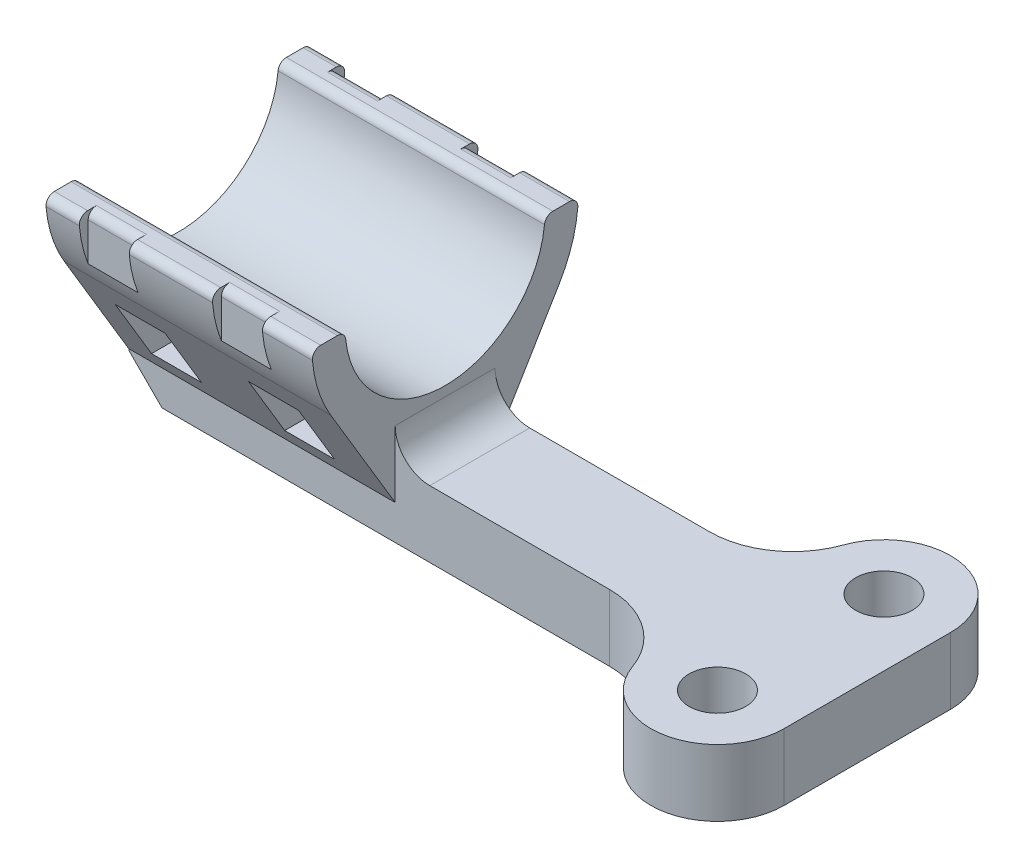
SolidWorks part; units mm, degrees
ref_plane "Front Plane" through (0, 0, 0) normal (0, 0, 1) x (1, 0, 0)
ref_plane "Top Plane" through (0, 0, 0) normal (0, 1, 0) x (1, 0, 0)
ref_plane "Right Plane" through (0, 0, 0) normal (1, 0, 0) x (0, 0, -1)
sketch "Sketch1" plane through (0, 0, 0) normal (0, 1, 0) x (1, 0, 0)
  line L0 (0, 0) -> (12.8697, 0)
  line L1 (0, 0) -> (0, 6)
  line L2 (0, 6) -> (12.8697, 6)
  line L3 (25.355, 8) -> (25.355, -2)
  arc A0 (12.8697, 6) -> (17.5838, 9.3333) centre (12.8697, 11) ccw
  arc A1 (25.355, 8) -> (17.5838, 9.3333) centre (21.355, 8) ccw
  arc A2 (17.5838, -3.3333) -> (25.355, -2) centre (21.355, -2) ccw
  arc A3 (17.5838, -3.3333) -> (12.8697, 0) centre (12.8697, -5) ccw
  circle A4 centre (21.355, -2) radius 1.7
  circle A5 centre (21.355, 8) radius 1.7
  dimension "D2" = 10
  dimension "D3" = 8
  dimension "D4" = 8
  dimension "D5" = 10
  dimension "D6" = 10
  dimension "D8" = 3.4
  dimension "D9" = 3.4
  dimension "D1" = 6
  dimension "D7" = 25.355
extrude "Boss-Extrude1" add sketch "Sketch1" along normal blind 4
sketch "Sketch2" plane through (0, 0, 0) normal (-1, 0, 0) x (0, 0, 1)
  line L0 (-6, 0) -> (0, 0)
  line L1 (0, 0) -> (0, 2.084)
  line L2 (0, 4) -> (0, 0) construction
  line L3 (-6, 0) -> (-6, 2.084)
  line L4 (-6, 4) -> (-6, 0) construction
  line L5 (-9.8672, 8.5551) -> (-6, 2.084)
  line L6 (0, 2.084) -> (3.8672, 8.5551)
  line L7 (-10.471, 12.5) -> (-9.4665, 12.5)
  line L8 (3.4665, 12.5) -> (4.471, 12.5)
  arc A0 (-8.9691, 12.0507) -> (2.9691, 12.0507) centre (-3, 12.659) ccw
  arc A1 (-10.9691, 11.9561) -> (-9.8672, 8.5551) centre (-3, 12.659) ccw
  arc A2 (3.8672, 8.5551) -> (4.9691, 11.9561) centre (-3, 12.659) ccw
  arc A3 (4.471, 12.5) -> (4.9691, 11.9561) centre (4.471, 12) cw
  arc A4 (2.9691, 12.0507) -> (3.4665, 12.5) centre (3.4665, 12) cw
  arc A5 (-8.9691, 12.0507) -> (-9.4665, 12.5) centre (-9.4665, 12) ccw
  arc A6 (-10.471, 12.5) -> (-10.9691, 11.9561) centre (-10.471, 12) ccw
  point P14 (-3, 0)
  point P22 (2.9979, 12.5)
  dimension "D2" = 12
  dimension "D3" = 12.659
  dimension "D4" = 16
  dimension "D6" = 0.5
  dimension "D1" = 2.084
  dimension "D5" = 12.5
extrude "Boss-Extrude2" add sketch "Sketch2" along normal blind 16
chamfer "Chamfer1" distance 2 angle 45 1 edges at (-16, 0, -3)
fillet "Fillet1" radius 2.08 1 edges at (0, 4, -3)
sketch "Sketch4" plane through (0, 0, 0) normal (0, 0, 1) x (1, 0, 0)
  line L0 (-16, 2.084) -> (-16, 8.5551) construction
  line L1 (-14, 5.289) -> (-11, 5.289)
  line L2 (-14, 5.289) -> (-14, 3.144)
  line L3 (-14, 3.144) -> (-11, 3.144)
  line L4 (-11, 5.289) -> (-11, 3.144)
  line L5 (-6, 5.289) -> (-3, 5.289)
  line L6 (-6, 5.289) -> (-6, 3.144)
  line L7 (-6, 3.144) -> (-3, 3.144)
  line L8 (-3, 5.289) -> (-3, 3.144)
  line L9 (-14, 0) -> (12.8697, 0) construction
  dimension "D1" = 3
  dimension "D2" = 3
  dimension "D3" = 2.145
  dimension "D4" = 2.145
  dimension "D5" = 2
  dimension "D6" = 5
  dimension "D7" = 3.144
  dimension "D8" = 3.144
extrude "Cut-Extrude1" cut sketch "Sketch4" against normal through all both and the other way through all
chamfer "Chamfer2" distance 1.705 angle 30 4 edges at (-12.5, 5.289, -7.9153) (-4.5, 5.289, -7.9153) (-4.5, 5.289, 1.9153) (-12.5, 5.289, 1.9153)
ref_plane "Plane3" through (-14, 0, 0) normal (-1, 0, 0) x (0, 0, 1)
sketch "Sketch5" plane through (-14, 0, 0) normal (-1, 0, 0) x (0, 0, 1)
  line L0 (4.439, 9.716) -> (4.439, 12)
  line L1 (4.471, 12.5) -> (3.4665, 12.5) construction
  line L2 (4.471, 12.5) -> (3.939, 12.5)
  line L3 (-9.939, 12.5) -> (-10.471, 12.5)
  line L4 (-9.4665, 12.5) -> (-10.471, 12.5) construction
  line L5 (-10.439, 12) -> (-10.439, 9.716)
  arc A0 (3.8672, 8.5551) -> (4.9691, 11.9561) centre (-3, 12.659) ccw construction
  arc A1 (4.439, 12) -> (3.939, 12.5) centre (3.939, 12) ccw
  arc A2 (4.9691, 11.9561) -> (4.471, 12.5) centre (4.471, 12) ccw construction
  arc A3 (4.439, 9.716) -> (4.9691, 11.9561) centre (-3, 12.659) ccw
  arc A4 (4.9691, 11.9561) -> (4.471, 12.5) centre (4.471, 12) ccw
  arc A5 (-10.9691, 11.9561) -> (-9.8672, 8.5551) centre (-3, 12.659) ccw construction
  arc A6 (-9.939, 12.5) -> (-10.439, 12) centre (-9.939, 12) ccw
  arc A7 (-10.471, 12.5) -> (-10.9691, 11.9561) centre (-10.471, 12) ccw construction
  arc A8 (-10.9691, 11.9561) -> (-10.439, 9.716) centre (-3, 12.659) ccw
  arc A9 (-10.471, 12.5) -> (-10.9691, 11.9561) centre (-10.471, 12) ccw
  point P10 (4.439, 12.5)
  point P21 (-10.439, 12.5)
  dimension "D3" = 0.5
  dimension "D5" = 0.5
  dimension "D1" = 90
  dimension "D2" = 2.784
  dimension "D4" = 2.784
extrude "Cut-Extrude2" cut sketch "Sketch5" against normal blind 3
ref_plane "Plane4" through (-6, 0, 0) normal (-1, 0, 0) x (0, 0, 1)
sketch "Sketch6" plane through (-6, 0, 0) normal (-1, 0, 0) x (0, 0, 1)
  line L0 (4.471, 12.5) -> (3.939, 12.5)
  line L1 (4.471, 12.5) -> (3.4665, 12.5) construction
  line L2 (4.439, 12) -> (4.439, 9.716)
  line L3 (-9.939, 12.5) -> (-10.471, 12.5)
  line L4 (-9.4665, 12.5) -> (-10.471, 12.5) construction
  line L5 (-10.439, 12) -> (-10.439, 9.716)
  arc A0 (3.8672, 8.5551) -> (4.9691, 11.9561) centre (-3, 12.659) ccw construction
  arc A1 (3.939, 12.5) -> (4.439, 12) centre (3.939, 12) cw
  arc A2 (4.9691, 11.9561) -> (4.471, 12.5) centre (4.471, 12) ccw construction
  arc A3 (4.439, 9.716) -> (4.9691, 11.9561) centre (-3, 12.659) ccw
  arc A4 (4.9691, 11.9561) -> (4.471, 12.5) centre (4.471, 12) ccw
  arc A5 (-10.9691, 11.9561) -> (-9.8672, 8.5551) centre (-3, 12.659) ccw construction
  arc A6 (-9.939, 12.5) -> (-10.439, 12) centre (-9.939, 12) ccw
  arc A7 (-10.471, 12.5) -> (-10.9691, 11.9561) centre (-10.471, 12) ccw construction
  arc A8 (-10.9691, 11.9561) -> (-10.439, 9.716) centre (-3, 12.659) ccw
  arc A9 (-10.471, 12.5) -> (-10.9691, 11.9561) centre (-10.471, 12) ccw
  point P11 (4.439, 12.5)
  point P21 (-10.439, 12.5)
  dimension "D2" = 0.5
  dimension "D4" = 0.5
  dimension "D1" = 2.784
  dimension "D3" = 2.784
extrude "Cut-Extrude3" cut sketch "Sketch6" against normal blind 3
